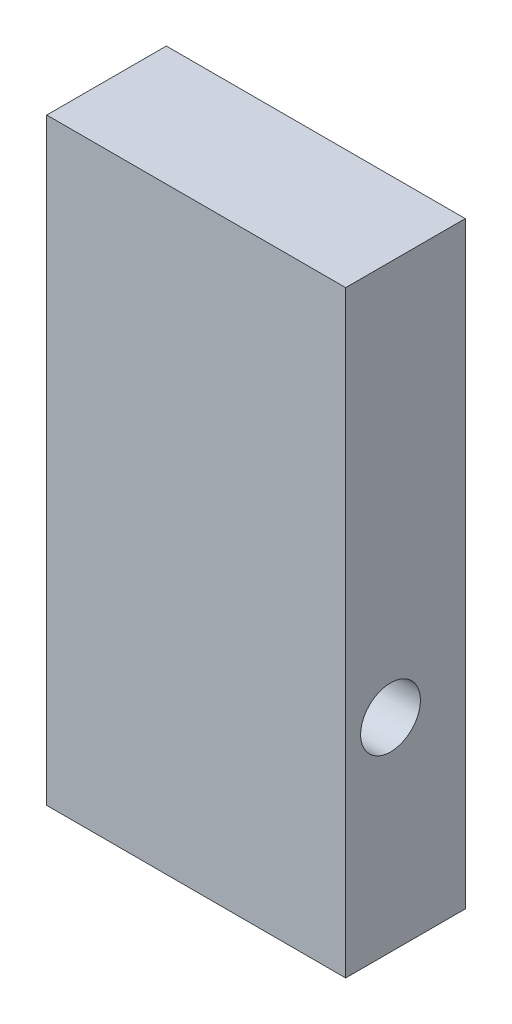
SolidWorks part; units mm, degrees
ref_plane "Front Plane" through (0, 0, 0) normal (0, 0, 1) x (1, 0, 0)
ref_plane "Top Plane" through (0, 0, 0) normal (0, 1, 0) x (1, 0, 0)
ref_plane "Right Plane" through (0, 0, 0) normal (1, 0, 0) x (0, 0, -1)
sketch "Sketch1" plane through (0, 0, 0) normal (0, 0, 1) x (1, 0, 0)
  line L1 (25, 50) -> (-25, 50)
  line L2 (25, 50) -> (25, -50)
  line L3 (25, -50) -> (-25, -50)
  line L4 (-25, 50) -> (-25, -50)
  line L5 (25, 50) -> (-25, -50) construction
  line L6 (25, -50) -> (-25, 50) construction
  point P0 (0, 0)
  dimension "D1" = 100
  dimension "D2" = 50
extrude "Boss-Extrude1" add sketch "Sketch1" along normal blind 20
sketch "Sketch3" plane through (-25, 0, 0) normal (-1, 0, 0) x (0, 0, 1)
  line L0 (0, 50) -> (0, -50) construction
  circle A0 centre (12.5, -16) radius 5
  point P4 (0, 0)
  dimension "D1" = 10
  dimension "D2" = 12.5
  dimension "D3" = 16
extrude "Cut-Extrude2" cut sketch "Sketch3" against normal blind 130
